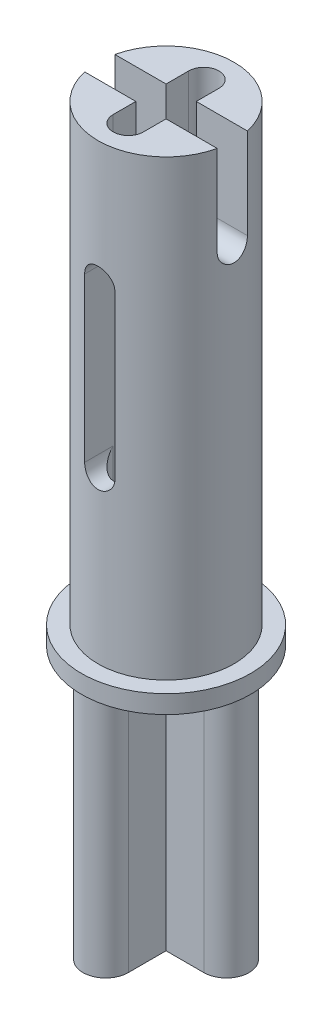
SolidWorks part; units mm, degrees
ref_plane "Front Plane" through (0, 0, 0) normal (0, 0, 1) x (1, 0, 0)
ref_plane "Top Plane" through (0, 0, 0) normal (0, 1, 0) x (1, 0, 0)
ref_plane "Right Plane" through (0, 0, 0) normal (1, 0, 0) x (0, 0, -1)
sketch "Sketch1" plane through (0, 0, 0) normal (0, 1, 0) x (1, 0, 0)
  circle A0 centre (0, 0) radius 2.25
  dimension "D1" = 4.5
extrude "Boss-Extrude1" add sketch "Sketch1" along normal blind 15
sketch "Sketch2" plane through (0, 0, 0) normal (0, -1, 0) x (1, 0, 0)
  circle A0 centre (0, 0) radius 2.8
  dimension "D1" = 5.6
extrude "Boss-Extrude2" add sketch "Sketch2" along normal blind 0.6
ref_plane "Plane1" through (0, 0, 10) normal (0, 0, 1) x (1, 0, 0)
ref_plane "Plane2" through (-2.25, 0, 0) normal (-1, 0, 0) x (0, 0, 1)
sketch "Sketch3" plane through (-2.25, 0, 0) normal (-1, 0, 0) x (0, 0, 1)
  line L0 (0, 0) -> (0, 12) construction
  line L1 (2.8, 0) -> (-2.8, 0) construction
  line L2 (0, 12) -> (0, 15) construction
  line L3 (2.25, 15) -> (-2.25, 15) construction
  line L4 (-0.5, 12) -> (-0.5, 15)
  line L5 (0.5, 12) -> (0.5, 15)
  line L6 (0, 0) -> (0, 5.5) construction
  arc A0 (-0.5, 12) -> (0.5, 12) centre (0, 12) ccw
  arc A1 (0.5, 15) -> (-0.5, 15) centre (0, 15) ccw
  point P4 (0, 13.5)
extrude "Cut-Extrude1" cut sketch "Sketch3" against normal through all
ref_plane "Plane3" through (-2.25, 0, 0) normal (-1, 0, 0) x (0, 0, 1)
ref_plane "Plane6" through (0, 0, 2.25) normal (0, 0, 1) x (1, 0, 0)
ref_plane "Plane7" through (0, 0, 100) normal (0, 0, 1) x (1, 0, 0)
sketch "Sketch6" plane through (0, 0, 2.25) normal (0, 0, 1) x (1, 0, 0)
  line L0 (0, 0) -> (0, 5.5) construction
  line L1 (0, 5.5) -> (0, 10.9) construction
  line L4 (-0.5, 5.5) -> (-0.5, 10.9)
  line L5 (0.5, 5.5) -> (0.5, 10.9)
  arc A2 (-0.5, 5.5) -> (0.5, 5.5) centre (0, 5.5) ccw
  arc A3 (0.5, 10.9) -> (-0.5, 10.9) centre (0, 10.9) ccw
  point P4 (0, 8.2)
extrude "Cut-Extrude5" cut sketch "Sketch6" against normal through all contours L5 A3 L4 A2
ref_plane "Plane8" through (0, 100, 0) normal (0, 1, 0) x (1, 0, 0)
sketch "Sketch8" plane through (0, 100, 0) normal (0, 1, 0) x (1, 0, 0)
  line L0 (0, -2.25) -> (0, -1.25) construction
  line L1 (-2.475, -2.25) -> (2.475, -2.25) construction
  line L2 (0, 2.25) -> (0, 1.25) construction
  line L3 (0, 1.25) -> (0, -1.25) construction
  line L4 (0.5, 1.25) -> (0.5, -1.25)
  line L5 (-0.5, 1.25) -> (-0.5, -1.25)
  arc A0 (2.1937, 0.5) -> (-2.1937, 0.5) centre (0, 0) ccw construction
  arc A1 (0.5, 1.25) -> (-0.5, 1.25) centre (0, 1.25) ccw
  arc A2 (-0.5, -1.25) -> (0.5, -1.25) centre (0, -1.25) ccw
  point P11 (0, 0)
  dimension "D1" = 1
  dimension "D2" = 1
extrude "Cut-Extrude6" cut sketch "Sketch8" against normal blind 100
sketch "Sketch11" plane through (0, -0.6, 0) normal (0, -1, 0) x (1, 0, 0)
  line L0 (0, -2.8) -> (0, 49997.2) construction
  line L1 (-2.8, 0) -> (49997.2, 0) construction
  line L2 (0, -2.8) -> (0, -2) construction
  line L3 (0, 2.8) -> (0, 2) construction
  line L4 (0, -2) -> (0, 2) construction
  line L5 (-0.75, -2) -> (-0.75, 2)
  line L6 (0.75, -2) -> (0.75, 2)
  line L7 (-2.8, 0) -> (-2, 0) construction
  line L8 (2.8, 0) -> (2, 0) construction
  line L9 (-2, 0) -> (2, 0) construction
  line L10 (-2, 0.75) -> (2, 0.75)
  line L11 (-2, -0.75) -> (2, -0.75)
  circle A0 centre (0, 0) radius 2.8 construction
  arc A1 (-0.75, -2) -> (0.75, -2) centre (0, -2) ccw
  arc A2 (0.75, 2) -> (-0.75, 2) centre (0, 2) ccw
  arc A3 (-2, 0.75) -> (-2, -0.75) centre (-2, 0) ccw
  arc A4 (2, -0.75) -> (2, 0.75) centre (2, 0) ccw
  point P11 (0, 0)
  point P20 (0, 0)
extrude "Boss-Extrude3" add sketch "Sketch11" along normal blind 8 contours L6 A2 L5 L10 | L5 L11 L6 L10 | L11 A4 L10 L6 | L10 A3 L11 L5 | L5 A1 L6 L11
